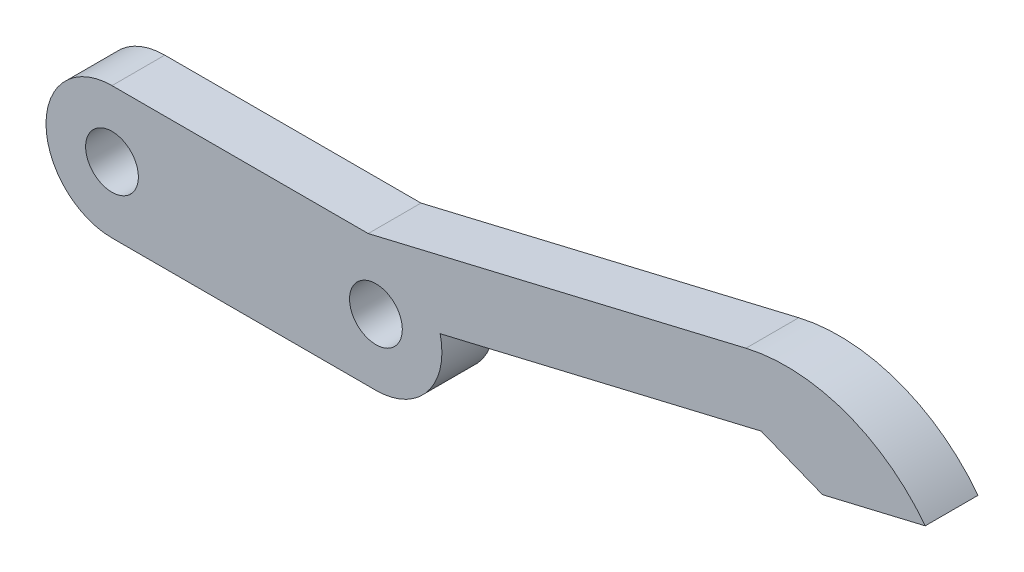
SolidWorks part; units mm, degrees
material "可锻铸铁"
ref_plane "前视基准面" through (0, 0, 0) normal (0, 0, 1) x (1, 0, 0)
ref_plane "上视基准面" through (0, 0, 0) normal (0, 1, 0) x (1, 0, 0)
ref_plane "右视基准面" through (0, 0, 0) normal (1, 0, 0) x (0, 0, -1)
sketch "草图1" plane through (0, 0, 0) normal (0, 0, 1) x (1, 0, 0)
  line L1 (-10, 5) -> (10, 5)
  line L3 (-10, -5) -> (10, -5)
  arc A0 (-10, 5) -> (-10, -5) centre (-10, 0) ccw
  arc A1 (10, -5) -> (10, 5) centre (10, 0) ccw
  point P0 (0, 0)
  dimension "D1" = 10
  dimension "D2" = 20
extrude "凸台-拉伸1" add sketch "草图1" along normal blind 4
sketch "草图2" plane through (0, 0, 4) normal (0, 0, 1) x (1, 0, 0)
  circle A0 centre (-10, 0) radius 2
  circle A1 centre (10, 0) radius 2
  dimension "D1" = 4
  dimension "D2" = 4
extrude "切除-拉伸1" cut sketch "草图2" against normal blind 4
sketch "草图3" plane through (0, 0, 4) normal (0, 0, 1) x (1, 0, 0)
  line L0 (11.9461, 0.4614) -> (39.1908, 6.9209)
  line L1 (9.5386, 1.9461) -> (8.8465, 4.8651)
  line L3 (8.8465, 4.8651) -> (38.0373, 11.7861)
  line L4 (39.1908, 6.9209) -> (43.8377, 5.0753)
  line L5 (43.8377, 5.0753) -> (51.6219, 6.9209)
  arc A0 (38.0373, 11.7861) -> (51.6219, 6.9209) centre (41.0898, -1.0887) cw
  arc A1 (11.9461, 0.4614) -> (9.5386, 1.9461) centre (10, 0) ccw
  dimension "D1" = 30
  dimension "D2" = 5
  dimension "D3" = 8
  dimension "D4" = 5
  dimension "D5" = 145
extrude "凸台-拉伸3" add sketch "草图3" against normal blind 4
